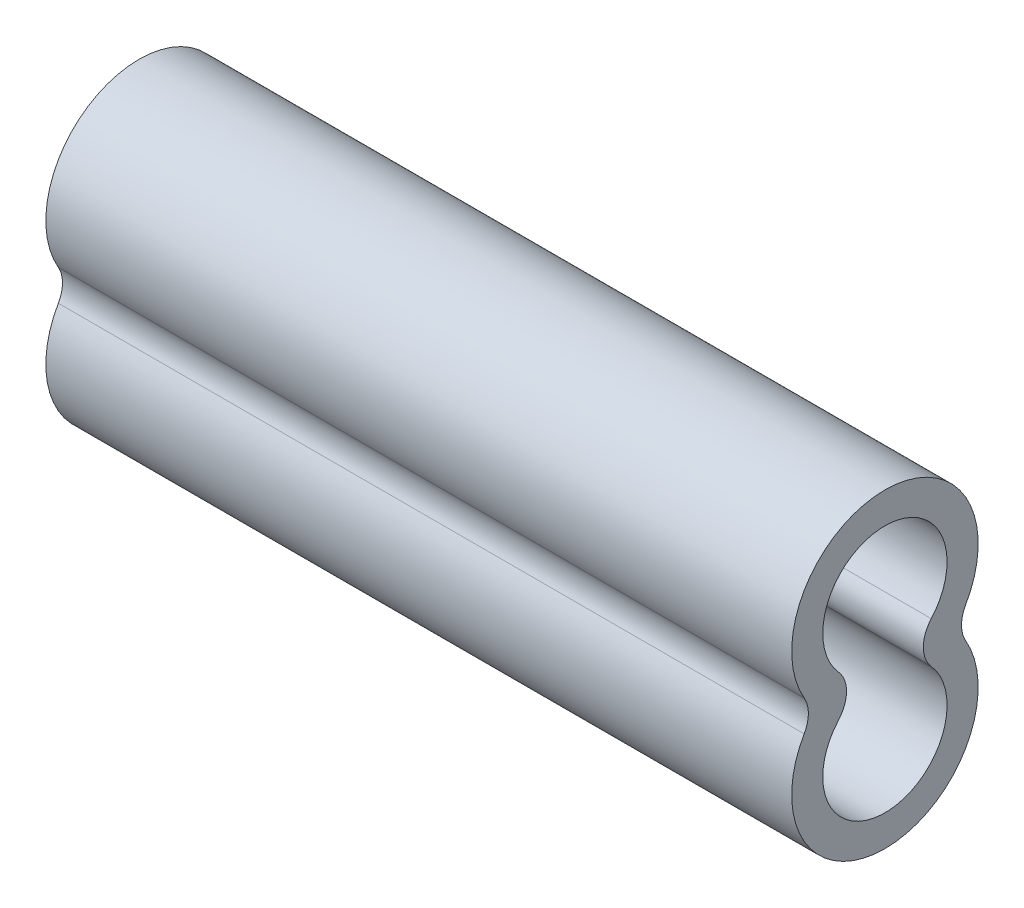
SolidWorks part; units mm, degrees
material "6061 Alloy"
ref_plane "Front Plane" through (0, 0, 0) normal (0, 0, 1) x (1, 0, 0)
ref_plane "Top Plane" through (0, 0, 0) normal (0, 1, 0) x (1, 0, 0)
ref_plane "Right Plane" through (0, 0, 0) normal (1, 0, 0) x (0, 0, -1)
sketch "Sketch1" plane through (0, 0, 0) normal (1, 0, 0) x (0, 0, -1)
  arc A0 (0.5413, 0.2646) -> (-0.6419, 0.2646) centre (-0.0503, 0.7938) ccw
  arc A1 (-0.6419, -0.2646) -> (0.5413, -0.2646) centre (-0.0503, -0.7937) ccw
  arc A2 (0.8371, 0) -> (-0.9378, 0) centre (-0.0503, 0.7938) ccw
  arc A3 (-0.9378, 0) -> (0.8371, 0) centre (-0.0503, -0.7937) ccw
  arc A4 (-0.6419, 0.2646) -> (-0.6419, -0.2646) centre (-0.9378, 0) cw
  arc A5 (0.5413, 0.2646) -> (0.5413, -0.2646) centre (0.8371, 0) ccw
  dimension "D1" = 0.7938
  dimension "D2" = 0.3969
extrude "Boss-Extrude1" add sketch "Sketch1" along normal blind 9.525
fillet "Fillet1" radius 0.3969 2 edges at (4.7625, 0, 0.9378) (4.7625, 0, -0.8371)
